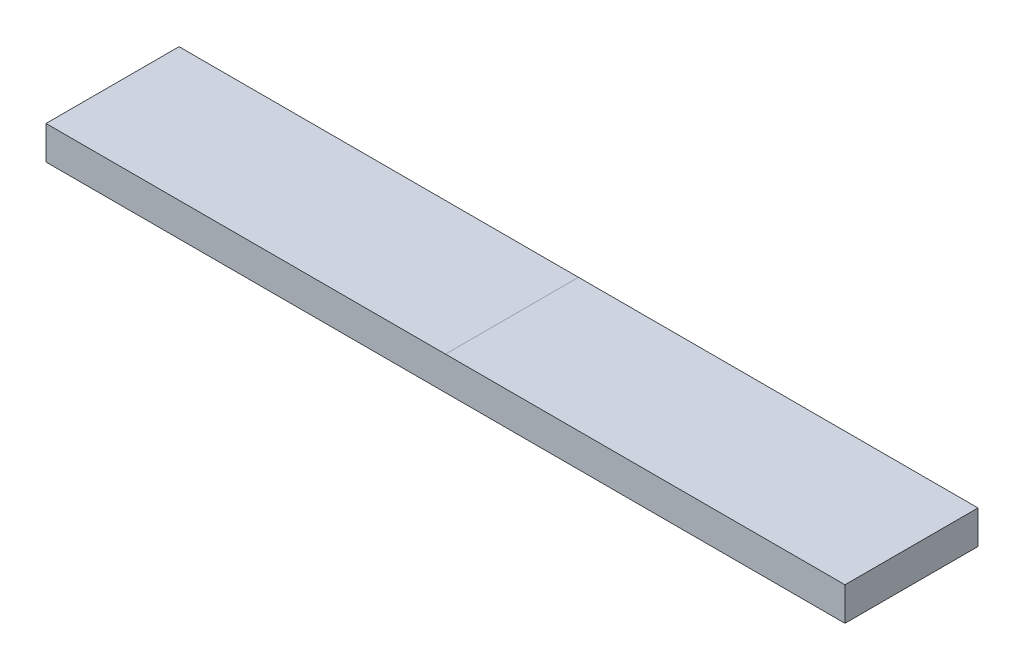
SolidWorks part; units mm, degrees
material "7075-O (SS)"
ref_plane "Front Plane" through (0, 0, 0) normal (0, 0, 1) x (1, 0, 0)
ref_plane "Top Plane" through (0, 0, 0) normal (0, 1, 0) x (1, 0, 0)
ref_plane "Right Plane" through (0, 0, 0) normal (1, 0, 0) x (0, 0, -1)
sketch "Sketch1" plane through (0, 0, 0) normal (1, 0, 0) x (0, 0, -1)
  line L1 (-12.6873, -3.1877) -> (12.6873, -3.1877)
  line L2 (-12.6873, -3.1877) -> (-12.6873, 3.1877)
  line L3 (-12.6873, 3.1877) -> (12.6873, 3.1877)
  line L4 (12.6873, -3.1877) -> (12.6873, 3.1877)
  line L5 (-12.6873, -3.1877) -> (12.6873, 3.1877) construction
  line L6 (-12.6873, 3.1877) -> (12.6873, -3.1877) construction
  point P0 (0, 0)
  dimension "D1" = 6.3754
  dimension "D2" = 25.3746
extrude "Boss-Extrude1" add sketch "Sketch1" along normal mid plane 152.4 contours L3 L4 L1 L2
ref_plane "Plane1" through (63.5, 0, 0) normal (1, 0, 0) x (0, 0, -1)
ref_plane "Plane2" through (-63.5, 0, 0) normal (1, 0, 0) x (0, 0, -1)
split line "Split Line1"
split line "Split Line3"
